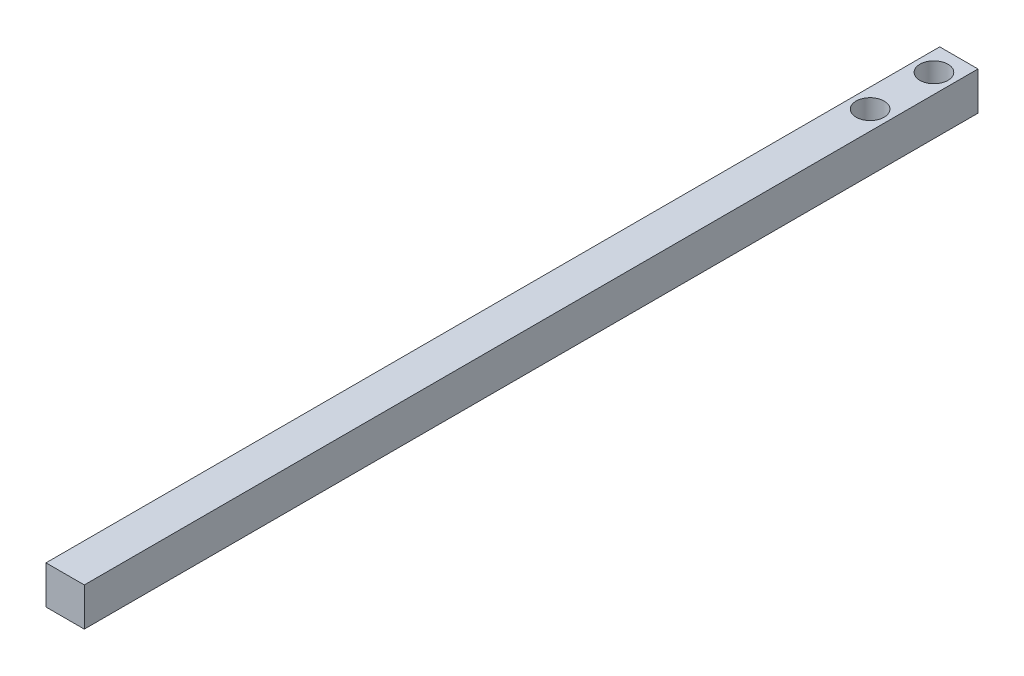
SolidWorks part; units mm, degrees
ref_plane "Front Plane" through (0, 0, 0) normal (0, 0, 1) x (1, 0, 0)
ref_plane "Top Plane" through (0, 0, 0) normal (0, 1, 0) x (1, 0, 0)
ref_plane "Right Plane" through (0, 0, 0) normal (1, 0, 0) x (0, 0, -1)
sketch "Sketch2" plane through (0, 0, 0) normal (0, 1, 0) x (1, 0, 0)
  line L1 (0, 0) -> (3, 0)
  line L2 (0, 0) -> (0, 70)
  line L3 (0, 70) -> (3, 70)
  line L4 (3, 0) -> (3, 70)
  dimension "D1" = 3
  dimension "D2" = 70
extrude "Boss-Extrude2" add sketch "Sketch2" along normal blind 3
sketch "Sketch4" plane through (0, 3, 0) normal (0, 1, 0) x (1, 0, 0)
  circle A0 centre (1.5, 68.0475) radius 1.1
  circle A1 centre (1.5, 63.0475) radius 1.1
  dimension "D1" = 2.2
  dimension "D2" = 2.2
  dimension "D3" = 5
extrude "Cut-Extrude1" cut sketch "Sketch4" against normal through all
equation "\"Hole Separation\"= 5mm"
equation "\"D3@Sketch4\"= \"Hole Separation\""
